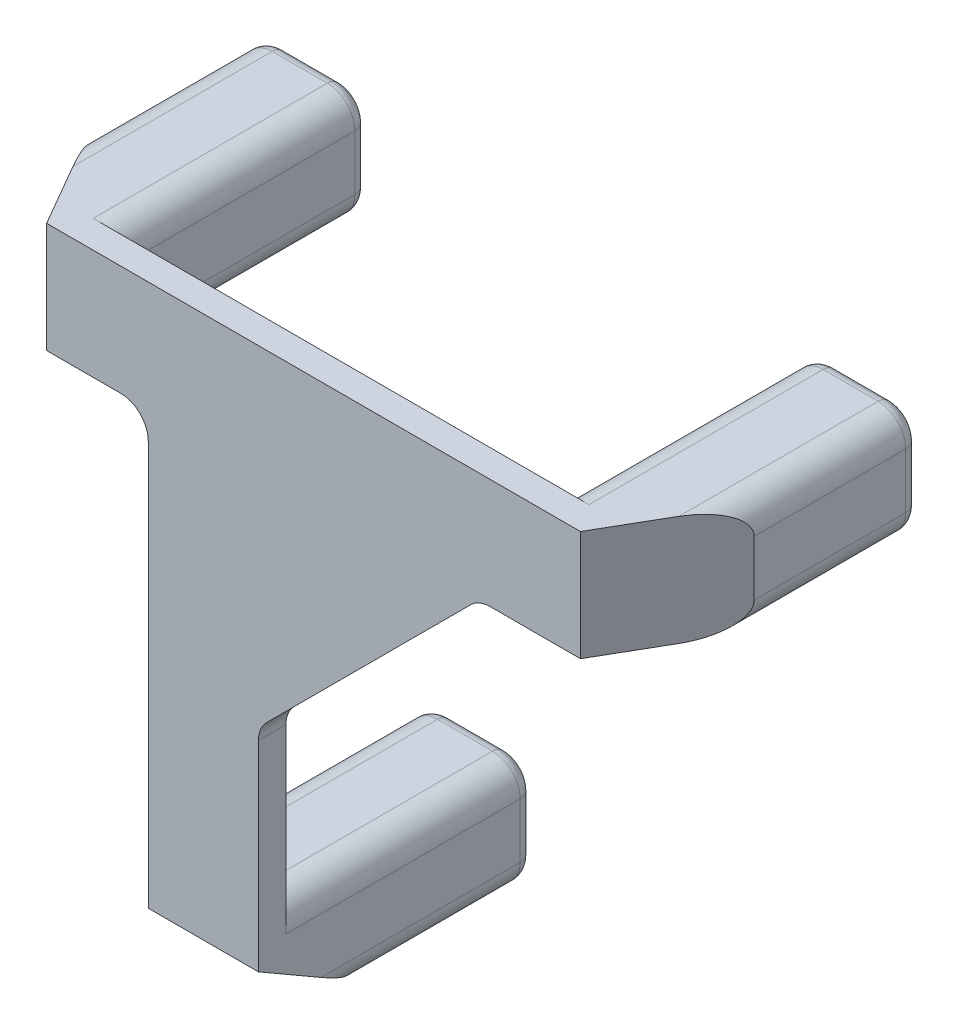
SolidWorks part; units mm, degrees
ref_plane "Front Plane" through (0, 0, 0) normal (0, 0, 1) x (1, 0, 0)
ref_plane "Top Plane" through (0, 0, 0) normal (0, 1, 0) x (1, 0, 0)
ref_plane "Right Plane" through (0, 0, 0) normal (1, 0, 0) x (0, 0, -1)
sketch "Sketch1" plane through (0, 0, 0) normal (0, 0, 1) x (1, 0, 0)
  line L0 (38.1, 0) -> (-38.1, 0)
  line L1 (-38.1, 0) -> (-38.1, -12.7)
  line L2 (-38.1, -12.7) -> (-19.05, -12.7)
  line L3 (-19.05, -12.7) -> (-19.05, -69.85)
  line L4 (-19.05, -69.85) -> (-6.35, -69.85)
  line L5 (-6.35, -69.85) -> (-6.35, -38.1)
  line L6 (19.05, -12.7) -> (38.1, -12.7)
  line L7 (38.1, -12.7) -> (38.1, 0)
  line L8 (19.05, -12.7) -> (-6.35, -38.1)
  point P4 (0, 0)
  point P10 (-6.35, -38.9501)
  point P13 (38.1, -11.7549)
  point P14 (0, 0)
  dimension "D1" = 12.7
  dimension "D2" = 76.2
  dimension "D3" = 57.15
  dimension "D4" = 19.05
  dimension "D5" = 12.7
  dimension "D6" = 19.05
  dimension "D7" = 135
extrude "Boss-Extrude1" add sketch "Sketch1" along normal blind 3.175
sketch "Sketch2" plane through (0, 0, 0) normal (0, 0, -1) x (-1, 0, 0)
  line L0 (-19.05, -12.7) -> (-38.1, -12.7) construction
  line L1 (-38.1, 0) -> (-25.4, 0)
  line L2 (-38.1, 0) -> (-38.1, -12.7)
  line L3 (-38.1, -12.7) -> (-25.4, -12.7)
  line L4 (-25.4, 0) -> (-25.4, -12.7)
  line L5 (38.1, -12.7) -> (19.05, -12.7) construction
  line L6 (38.1, 0) -> (25.4, 0)
  line L7 (38.1, 0) -> (38.1, -12.7)
  line L8 (38.1, -12.7) -> (25.4, -12.7)
  line L9 (25.4, 0) -> (25.4, -12.7)
  line L10 (6.35, -69.85) -> (6.35, -38.1) construction
  line L11 (19.05, -69.85) -> (6.35, -69.85)
  line L12 (19.05, -69.85) -> (19.05, -57.15)
  line L13 (19.05, -57.15) -> (6.35, -57.15)
  line L14 (6.35, -69.85) -> (6.35, -57.15)
extrude "Boss-Extrude2" add sketch "Sketch2" along normal blind 28.575
sketch "Sketch3" plane through (0, 0, -28.575) normal (0, 0, -1) x (-1, 0, 0)
  line L0 (-38.1, -12.7) -> (-25.4, -12.7) construction
  line L1 (-38.1, 0) -> (-38.1, -12.7) construction
  line L2 (38.1, 0) -> (25.4, 0) construction
  line L3 (38.1, -12.7) -> (38.1, 0) construction
  line L4 (19.05, -57.15) -> (6.35, -57.15) construction
  line L5 (19.05, -69.85) -> (19.05, -57.15) construction
  circle A0 centre (-31.75, -6.35) radius 2.5
  circle A1 centre (31.75, -6.35) radius 2.5
  circle A2 centre (12.7, -63.5) radius 2.5
  point P6 (0, 0)
  point P7 (0, 0)
  point P10 (-31.75, -12.7)
  point P11 (0, 0)
  point P14 (-38.1, -6.35)
  point P17 (31.75, 0)
  point P20 (38.1, -6.35)
  point P23 (12.7, -57.15)
  point P26 (19.05, -63.5)
  dimension "D1" = 5
extrude "Cut-Extrude1" cut sketch "Sketch3" against normal blind 10
chamfer "Chamfer1" distance 12.7 angle 30 3 edges at (38.1, -6.35, 3.175) (-12.7, -69.85, 3.175) (-38.1, -6.35, 3.175)
fillet "Fillet1" radius 3.175 3 edges at (19.05, -12.7, 1.5875) (-6.35, -38.1, 1.5875) (-19.05, -12.7, 1.5875)
fillet "Fillet2" radius 3.175 12 edges at (-19.05, -57.15, -14.2875) (-19.05, -69.85, -19.05) (-6.35, -69.85, -19.05) (-6.35, -57.15, -14.2875) (38.1, -12.7, -19.05) (38.1, 0, -19.05) (25.4, 0, -14.2875) (25.4, -12.7, -14.2875) (-25.4, 0, -14.2875) (-25.4, -12.7, -14.2875) (-38.1, 0, -19.05) (-38.1, -12.7, -19.05)
fillet "Fillet4" radius 1.5875 24 edges at (-26.3299, -0.9299, -28.575) (-31.75, 0, -28.575) (-37.1701, -0.9299, -28.575) (-38.1, -6.35, -28.575) (-37.1701, -11.7701, -28.575) (-31.75, -12.7, -28.575) (-26.3299, -11.7701, -28.575) (-25.4, -6.35, -28.575) (-12.7, -57.15, -28.575) (-18.1201, -58.0799, -28.575) (-19.05, -63.5, -28.575) (-18.1201, -68.9201, -28.575) (-12.7, -69.85, -28.575) (-7.2799, -68.9201, -28.575) (-6.35, -63.5, -28.575) (-7.2799, -58.0799, -28.575) (26.3299, -11.7701, -28.575) (25.4, -6.35, -28.575) (26.3299, -0.9299, -28.575) (31.75, -12.7, -28.575) (37.1701, -11.7701, -28.575) (38.1, -6.35, -28.575) (37.1701, -0.9299, -28.575) (31.75, 0, -28.575)
